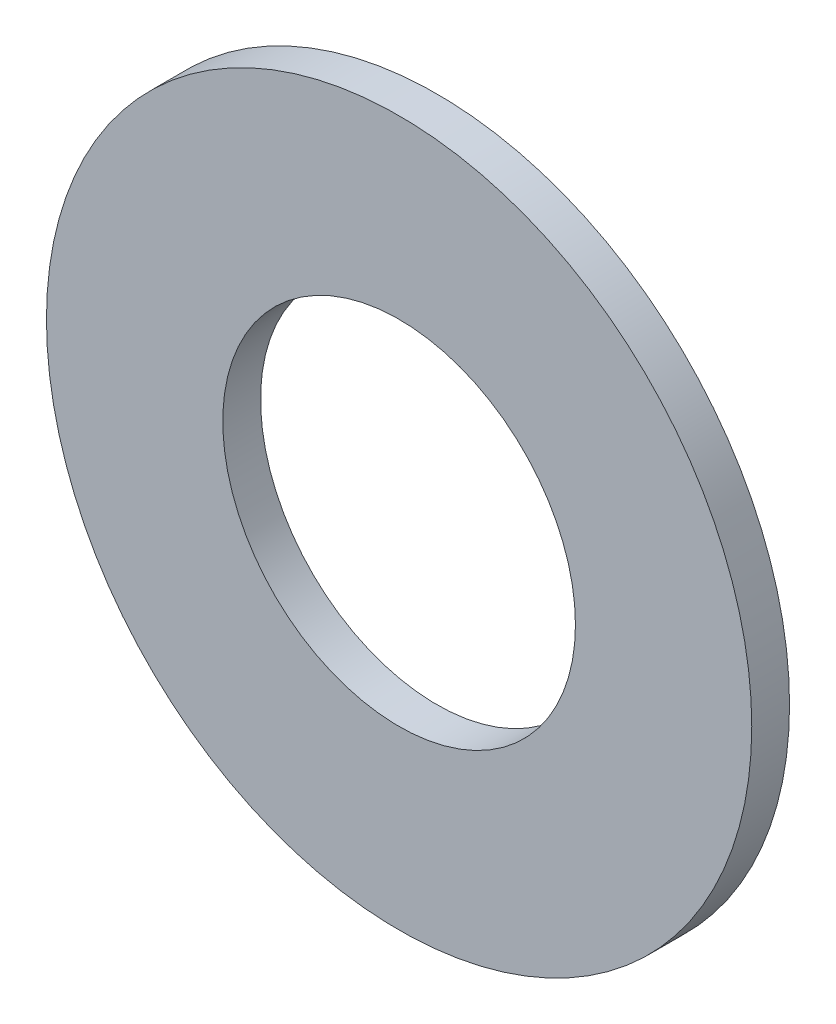
SolidWorks part; units mm, degrees
material "PMMA"
ref_plane "Front Plane" through (0, 0, 0) normal (0, 0, 1) x (1, 0, 0)
ref_plane "Top Plane" through (0, 0, 0) normal (0, 1, 0) x (1, 0, 0)
ref_plane "Right Plane" through (0, 0, 0) normal (1, 0, 0) x (0, 0, -1)
sketch "Sketch1" plane through (0, 0, 0) normal (0, 0, 1) x (1, 0, 0)
  circle A0 centre (0, 0) radius 7
  circle A1 centre (0, 0) radius 14
  dimension "D1" = 14
  dimension "D2" = 28
extrude "Boss-Extrude1" add sketch "Sketch1" along normal blind 1.5
